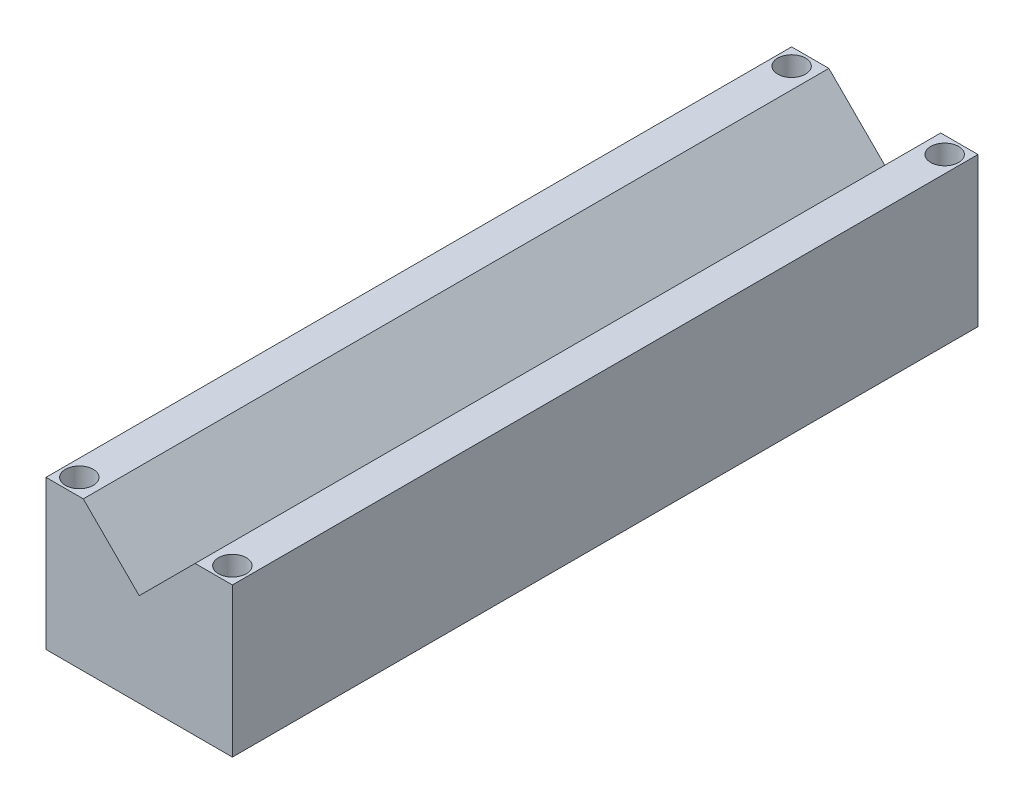
SolidWorks part; units mm, degrees
ref_plane "Alzado" through (0, 0, 0) normal (0, 0, 1) x (1, 0, 0)
ref_plane "Planta" through (0, 0, 0) normal (0, 1, 0) x (1, 0, 0)
ref_plane "Vista lateral" through (0, 0, 0) normal (1, 0, 0) x (0, 0, -1)
sketch "Croquis2" plane through (0, 0, 0) normal (0, 0, 1) x (1, 0, 0)
  line L1 (0, 0) -> (63.5, 0)
  line L2 (0, 0) -> (0, 50.8)
  line L3 (0, 50.8) -> (63.5, 50.8)
  line L4 (63.5, 0) -> (63.5, 50.8)
  dimension "D1" = 50.8
  dimension "D2" = 63.5
extrude "Saliente-Extruir1" add sketch "Croquis2" against normal blind 254
sketch "Croquis5" plane through (0, 50.8, 0) normal (0, 1, 0) x (1, 0, 0)
  line L0 (63.5, 0) -> (0, 0) construction
  line L1 (63.5, 254) -> (63.5, 0) construction
  line L2 (31.75, 0) -> (31.75, 254) construction
  line L3 (63.5, 254) -> (0, 254) construction
  line L4 (63.5, 127) -> (0, 127) construction
  line L5 (0, 254) -> (0, 0) construction
  circle A0 centre (57.82, 5.675) radius 3.175
  circle A1 centre (5.68, 5.675) radius 3.175
  circle A2 centre (5.68, 248.325) radius 3.175
  circle A3 centre (57.82, 248.325) radius 3.175
  dimension "D1" = 6.35
  dimension "D2" = 5.675
  dimension "D3" = 5.68
extrude "Cortar-Extruir3" cut sketch "Croquis5" against normal up to surface (50.8 mm away) up to face at (31.75, 0, -127)
sketch "Croquis10" plane through (0, 50.8, 0) normal (0, 1, 0) x (1, 0, 0)
  circle A0 centre (57.82, 5.675) radius 4.75
  circle A1 centre (5.68, 5.675) radius 4.75
  dimension "D1" = 9.5
  dimension "D2" = 9.5
extrude "Cortar-Extruir5" cut sketch "Croquis10" against normal blind 8
sketch "Croquis11" plane through (0, 0, 0) normal (0, 0, 1) x (1, 0, 0)
  line L0 (31.75, 50.8) -> (31.75, 0) construction
  line L1 (63.5, 50.8) -> (0, 50.8) construction
  line L2 (0, 0) -> (63.5, 0) construction
  line L3 (31.75, 31.75) -> (50.8, 50.8)
  line L4 (31.75, 31.75) -> (12.7, 50.8)
  line L5 (12.7, 50.8) -> (50.8, 50.8)
  dimension "D1" = 19.05
  dimension "D2" = 45
  dimension "D3" = 45
extrude "Cortar-Extruir6" cut sketch "Croquis11" against normal up to surface (254 mm away) up to face at (31.75, 25.4, -254)
sketch "Croquis12" plane through (0, 50.8, 0) normal (0, 1, 0) x (1, 0, 0)
  circle A0 centre (57.82, 248.325) radius 4.75
  circle A1 centre (5.68, 248.325) radius 4.75
  dimension "D1" = 9.5
  dimension "D2" = 9.5
extrude "Cortar-Extruir7" cut sketch "Croquis12" against normal blind 8
